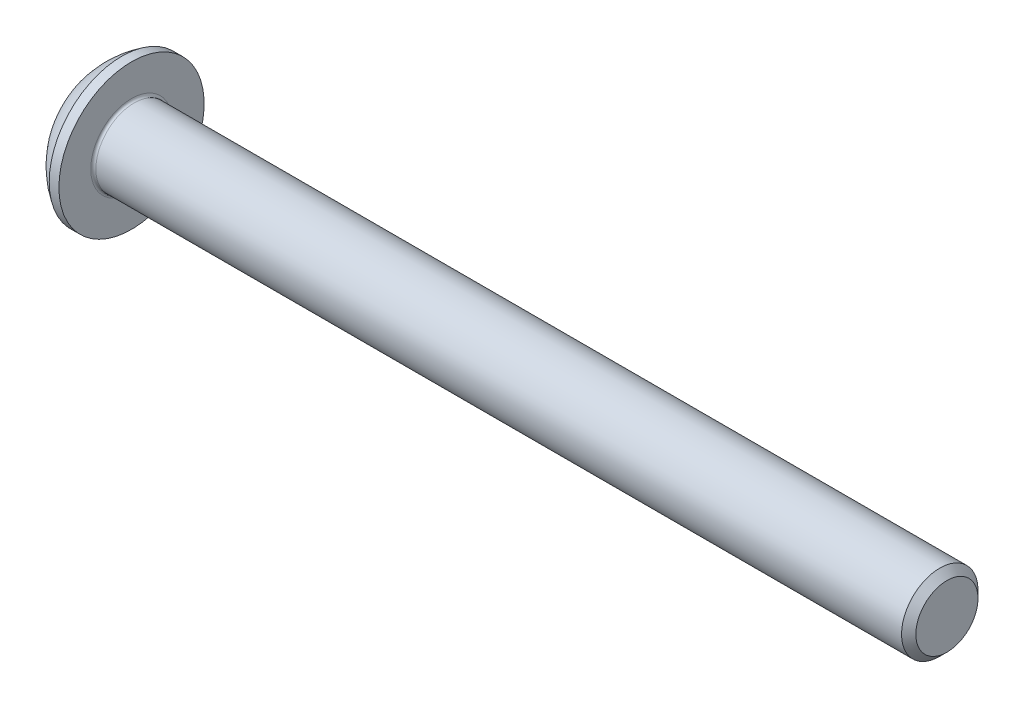
SolidWorks part; units mm, degrees
ref_plane "Plane1" through (0, 0, 0) normal (0, 0, 1) x (1, 0, 0)
ref_plane "Plane2" through (0, 0, 0) normal (0, 1, 0) x (1, 0, 0)
ref_plane "Plane3" through (0, 0, 0) normal (1, 0, 0) x (0, 0, -1)
sketch "BodySke" plane through (0, 0, 0) normal (0, 0, 1) x (1, 0, 0)
  line L0 (33.65, 0) -> (33.65, 1.2195)
  line L1 (33.3695, 1.5) -> (1.65, 1.5)
  line L2 (1.65, 1.5) -> (1.65, 2.85)
  line L3 (1.65, 2.85) -> (1.27, 2.85)
  line L4 (0, 0) -> (101.6, 0) construction
  line L5 (1.65, -2.85) -> (1.27, -2.85) construction
  line L6 (55.6768, -1.5) -> (1.65, -1.5) construction
  line L7 (33.65, 0) -> (0, 0)
  line L8 (0, 1.425) -> (0, -1.425) construction
  line L9 (0, 0) -> (0, 1.425)
  line L10 (33.65, 1.2195) -> (33.3695, 1.5)
  line L11 (33.65, -1.2195) -> (33.3695, -1.5) construction
  line L12 (2.15, 9.525) -> (2.15, -1.5) construction
  line L13 (1.65, 9.525) -> (1.65, -1.5) construction
  arc A1 (0, 1.425) -> (1.27, 2.85) centre (3.0334, 0) cw
  dimension "Diameter" = 3
  dimension "Length" = 32
  dimension "Head_dia" = 5.7
  dimension "D1" = 2.85
  dimension "Head_ht" = 1.65
  dimension "Head_side_ht" = 0.38
  dimension "Minor_dia" = 2.439
  dimension "Body_ch_ang" = 45
  dimension "Advance" = 0.5
  dimension "Thread_nom" = 32
revolve "BaseBody" add sketch "BodySke" angle 360 about L4
cosmetic thread "ThreadCosmetic" [suppressed] parameters "Thread_length"=31, "Thread_minor"=2.439
fillet "Fillet1" radius 0.1 1 edges at (1.65, 0, 1.5)
sketch "Sketch2" plane through (0, 0, 0) normal (0, 0, 1) x (1, 0, 0)
  line L0 (0, 1) -> (1.04, 1)
  line L1 (1.04, 1) -> (1.6174, 0)
  line L3 (1.6174, 0) -> (0, 0)
  line L4 (0, 0) -> (0, 1)
  line L5 (0, -1) -> (1.04, -1) construction
  line L6 (0, 0) -> (47.625, 0) construction
  dimension "D2" = 60
  dimension "PreBroach_depth" = 1.04
  dimension "PreBroach_dia" = 2
revolve "PreBroach" cut sketch "Sketch2" angle 360 about L6
sketch "Sketch3" plane through (0, 0, 0) normal (1, 0, 0) x (0, 0, -1)
  line L0 (-1, -0.5774) -> (-1, 0.5774)
  line L1 (-1, 0.5774) -> (0, 1.1547)
  line L2 (0, 1.1547) -> (1, 0.5774)
  line L3 (1, 0.5774) -> (1, -0.5774)
  line L4 (1, -0.5774) -> (0, -1.1547)
  line L5 (0, -1.1547) -> (-1, -0.5774)
  dimension "Hex_size" = 2
  dimension "D3" = 2
  dimension "D1" = 1
  dimension "D2" = 1
extrude "Hex" cut sketch "Sketch3" along normal blind 1.04
sketch "ThdSchSke" plane through (0, 0, 0) normal (0, 0, 1) x (1, 0, 0)
  line L0 (2.65, -1.2195) -> (2.4536, -1.5)
  line L1 (2.65, -1.2195) -> (2.8464, -1.5)
  line L2 (2.8464, -1.5) -> (2.8464, -1.875)
  line L3 (-3.175, 0) -> (5.1513, 0) construction
  line L5 (2.8464, -1.875) -> (2.4536, -1.875)
  line L6 (2.4536, -1.875) -> (2.4536, -1.5)
  dimension "Diameter" = 3
  dimension "Thread_minor" = 2.439
  dimension "SideAngle" = 55
  dimension "VeeAngle" = 70
  dimension "Overcut" = 3.75
  dimension "Start" = 2.65
revolve "ThreadSchematic" [suppressed] cut sketch "ThdSchSke" angle 360 about L3
pattern_linear "ThdSchPat" [suppressed]
equation "\"D1@BodySke\" = \"Head_dia@BodySke\" * .5"
equation "\"Thread_minor@ThreadCosmetic\" = \"Minor_dia@BodySke\""
equation "\"D1@Sketch3\" = \"Hex_size@Sketch3\" / 2"
equation "\"D2@Sketch3\" = \"D1@Sketch3\""
equation "\"D3@Sketch3\" = \"Hex_size@Sketch3\""
equation "\"Thread_length@ThreadCosmetic\" = ((sgn( (\"Length@BodySke\" - \"Advance@BodySke\" * 2.0) - \"Thread_nom@BodySke\" )-1)*( (\"Length@BodySke\" - \"Advance@BodySke\" * 2.0) - \"Thread_nom@BodySke\" ))/-2+ \"Thread_nom@BodySke\""
equation "\"Thread_minor@ThdSchSke\" = \"Minor_dia@BodySke\""
equation "\"Diameter@ThdSchSke\" = \"Diameter@BodySke\""
equation "\"Overcut@ThdSchSke\" = \"Diameter@BodySke\" * 1.25"
equation "\"Start@ThdSchSke\" = \"Head_ht@BodySke\" + \"Length@BodySke\" - \"Thread_length@ThreadCosmetic\"  '---Non-countersunk---"
equation "\"Num_threads@ThdSchPat\" = int( \"Thread_length@ThreadCosmetic\" / \"Advance@BodySke\" + 0.999 )  + 1"
equation "\"Advance@ThdSchPat\" = \"Thread_length@ThreadCosmetic\" /  (\"Num_threads@ThdSchPat\" - 1) 'relax it"
equation "\"Num_threads@ThdSchPat\" = \"Num_threads@ThdSchPat\" - sgn( \"Num_threads@ThdSchPat\" - 1) '---chamfered tips only---"
